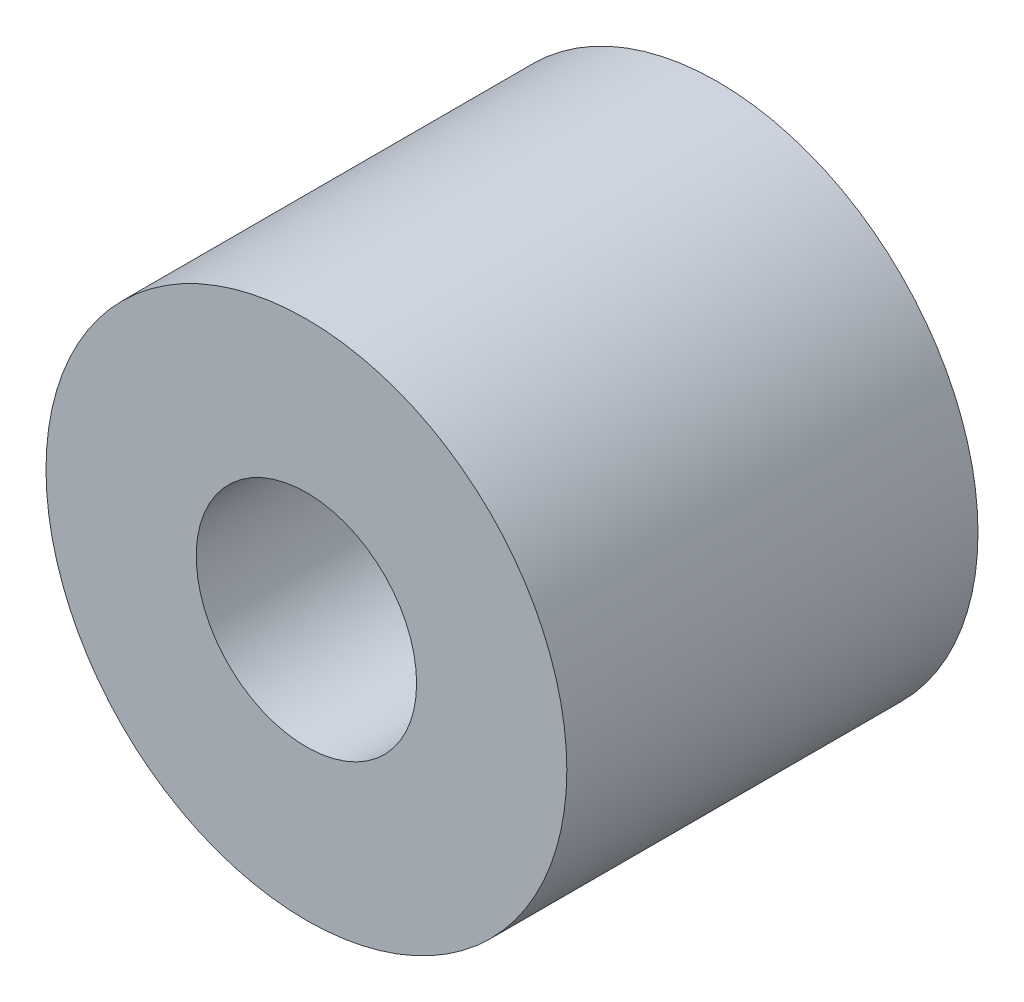
SolidWorks part; units mm, degrees
ref_plane "Front Plane" through (0, 0, 0) normal (0, 0, 1) x (1, 0, 0)
ref_plane "Top Plane" through (0, 0, 0) normal (0, 1, 0) x (1, 0, 0)
ref_plane "Right Plane" through (0, 0, 0) normal (1, 0, 0) x (0, 0, -1)
sketch "Sketch1" plane through (0, 0, 0) normal (0, 0, 1) x (1, 0, 0)
  circle A0 centre (0, 0) radius 6.0325
  dimension "D1" = 12.065
extrude "Boss-Extrude1" add sketch "Sketch1" along normal mid plane 9.525
sketch "Sketch2" plane through (0, 0, 4.7625) normal (0, 0, 1) x (1, 0, 0)
  point P0 (0, 0)
hole_wizard "Tap Drill for 1/4-20 Tap1" positions "Sketch2" profile "Sketch3" hole size "1/4-20" standard "ANSI Inch" end condition through all
sketch "Sketch3" plane through (0, 0, 4.7625) normal (1, 0, 0) x (0, -1, 0)
  line L0 (0, 0) -> (0, 9.525)
  line L1 (0, 9.525) -> (2.5527, 9.525)
  line L2 (2.5527, 9.525) -> (2.5527, 0)
  line L5 (2.5527, 0) -> (0, 0)
  line L11 (0, -6.35) -> (0, 107.95) construction
  dimension "Thru Hole Dia." = 5.1054
  dimension "Thru Hole Depth" = 9.525
cosmetic thread "Cosmetic Thread1" parameters "D2"=6.1054
equation "\"AIRFRAME_OD\"= 5.15in"
equation "\"AIRFRAME_ID\"= 5.00in"
equation "\"FLAT_T\"= 0.125in"
equation "\"NOSE_EXP_L\"= 27in"
equation "\"NOSE_SHOULDER_L\"= 5in"
equation "\"MAIN_L\"= 30in"
equation "\"RECO_COUP_L\"= 10in"
equation "\"RECO_SWITCH_L\"= 2in"
equation "\"DROGUE_L\"= 20in"
equation "\"ATS_FORE_COUP_L\"= 5.5in"
equation "\"ATS_AFT_COUP_L\"= 4.5in"
equation "\"LOWER_L\"= 30in"
equation "\"FIN_N\"= 4"
equation "\"CR_AFT_X\"= 0.5in"
equation "\"CR_FORE_X\"= 9.25in"
